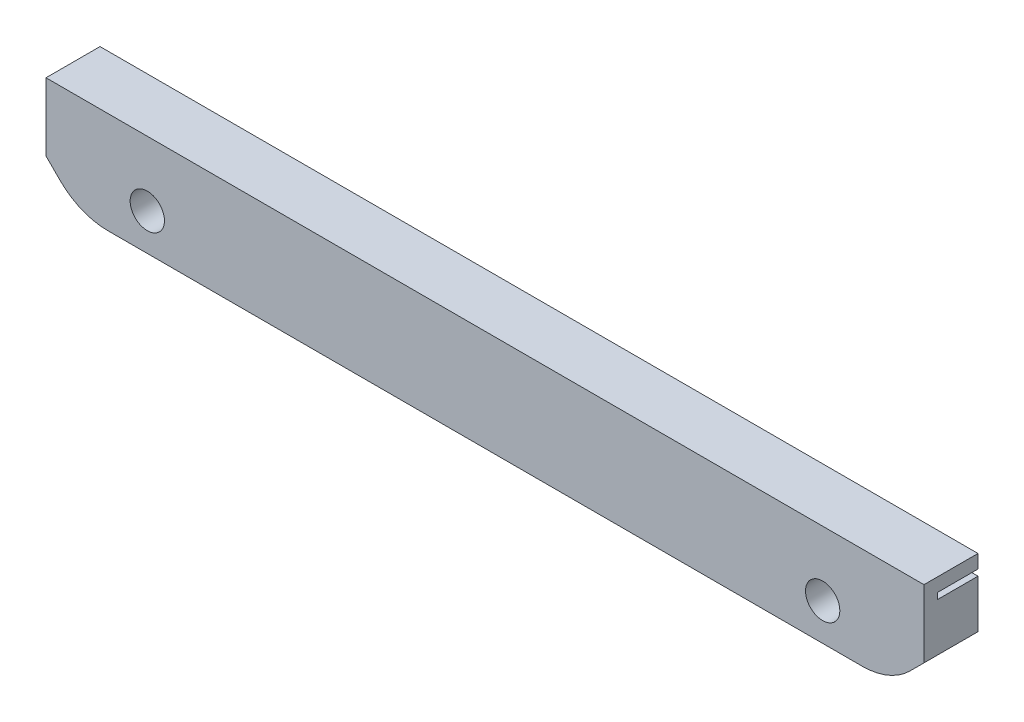
SolidWorks part; units mm, degrees
ref_plane "Front Plane" through (0, 0, 0) normal (0, 0, 1) x (1, 0, 0)
ref_plane "Top Plane" through (0, 0, 0) normal (0, 1, 0) x (1, 0, 0)
ref_plane "Right Plane" through (0, 0, 0) normal (1, 0, 0) x (0, 0, -1)
sketch "Sketch2" plane through (0, 0, 0) normal (0, 0, 1) x (1, 0, 0)
  line L0 (-115, -10) -> (-115, 135.26) construction
  line L1 (-115, 69.83) -> (15, 69.83)
  line L5 (15, 69.83) -> (15, 54.7963)
  line L6 (15, 54.7963) -> (-115, 54.7963)
  line L7 (-109.2, 69.93) -> (-66.71, 69.93) construction
  line L8 (-115, 54.7963) -> (-115, 69.83)
  circle A0 centre (-100, 60.26) radius 2.54
  circle A1 centre (0, 60.26) radius 2.54
  point P4 (-50, 29.465)
  dimension "D2" = 5.08
  dimension "D3" = 5.08
  dimension "D1" = 0.1
extrude "Boss-Extrude1" add sketch "Sketch2" along normal blind 6
sketch "Sketch3" plane through (0, 0, 6) normal (0, 0, 1) x (1, 0, 0)
  line L0 (15, 69.83) -> (-115, 69.83) construction
  line L5 (-59.5285, 67.83) -> (-59.5285, 59.3047)
  line L6 (-103.0137, 66.919) -> (-102.0149, 66.919)
  line L7 (-102.0149, 66.919) -> (-102.0149, 66.2967)
  line L8 (-102.0149, 66.2967) -> (-101.016, 66.2967)
  line L9 (-101.016, 66.2967) -> (-101.016, 66.919)
  line L10 (-101.016, 66.919) -> (-100.0172, 66.919)
  line L11 (-100.0172, 66.919) -> (-100.0172, 66.2967)
  line L12 (-100.0172, 66.2967) -> (-99.0183, 66.2967)
  line L13 (-99.0183, 66.2967) -> (-99.0183, 66.919)
  line L14 (-99.0183, 66.919) -> (-98.0195, 66.919)
  line L15 (-98.0195, 66.919) -> (-98.0195, 66.2967)
  line L16 (-98.0195, 66.2967) -> (-97.0206, 66.2967)
  line L17 (-97.0206, 66.2967) -> (-97.0206, 66.919)
  line L18 (-97.0206, 66.919) -> (-96.0218, 66.919)
  line L19 (-96.0218, 66.919) -> (-96.0218, 66.2967)
  line L20 (-96.0218, 66.2967) -> (-95.0229, 66.2967)
  line L21 (-95.0229, 66.2967) -> (-95.0229, 66.919)
  line L22 (-95.0229, 66.919) -> (-94.024, 66.919)
  line L23 (-94.024, 66.919) -> (-94.024, 66.2967)
  line L24 (-94.024, 66.2967) -> (-93.0252, 66.2967)
  line L25 (-93.0252, 66.2967) -> (-93.0252, 66.919)
  line L26 (-93.0252, 66.919) -> (-92.0263, 66.919)
  line L27 (-92.0263, 66.919) -> (-92.0263, 66.2967)
  line L28 (-92.0263, 66.2967) -> (-91.0275, 66.2967)
  line L29 (-91.0275, 66.2967) -> (-91.0275, 66.919)
  line L30 (-91.0275, 66.919) -> (-90.0286, 66.919)
  line L31 (-90.0286, 66.919) -> (-90.0286, 66.2967)
  line L32 (-90.0286, 66.2967) -> (-89.0298, 66.2967)
  line L33 (-89.0298, 66.2967) -> (-89.0298, 66.919)
  line L34 (-89.0298, 66.919) -> (-88.0309, 66.919)
  line L35 (-88.0309, 66.919) -> (-88.0309, 66.2967)
  line L36 (-88.0309, 66.2967) -> (-87.0321, 66.2967)
  line L37 (-87.0321, 66.2967) -> (-87.0321, 66.919)
  line L38 (-87.0321, 66.919) -> (-86.0332, 66.919)
  line L39 (-86.0332, 66.919) -> (-86.0332, 66.2967)
  line L40 (-86.0332, 66.2967) -> (-85.0344, 66.2967)
  line L41 (-85.0344, 66.2967) -> (-85.0344, 66.919)
  line L42 (-85.0344, 66.919) -> (-84.0355, 66.919)
  line L43 (-84.0355, 66.919) -> (-84.0355, 66.2967)
  line L44 (-84.0355, 66.2967) -> (-83.0366, 66.2967)
  line L45 (-83.0366, 66.2967) -> (-83.0366, 66.919)
  line L46 (-83.0366, 66.919) -> (-82.0378, 66.919)
  line L47 (-82.0378, 66.919) -> (-82.0378, 66.2967)
  line L48 (-82.0378, 66.2967) -> (-81.0389, 66.2967)
  line L49 (-81.0389, 66.2967) -> (-81.0389, 66.919)
  line L50 (-81.0389, 66.919) -> (-80.0401, 66.919)
  line L51 (-80.0401, 66.919) -> (-80.0401, 66.2967)
  line L52 (-80.0401, 66.2967) -> (-79.0412, 66.2967)
  line L53 (-79.0412, 66.2967) -> (-79.0412, 66.919)
  line L54 (-79.0412, 66.919) -> (-78.0424, 66.919)
  line L55 (-78.0424, 66.919) -> (-78.0424, 66.2967)
  line L56 (-78.0424, 66.2967) -> (-77.0435, 66.2967)
  line L57 (-77.0435, 66.2967) -> (-77.0435, 66.919)
  line L58 (-77.0435, 66.919) -> (-76.0447, 66.919)
  line L59 (-76.0447, 66.919) -> (-76.0447, 66.2967)
  line L60 (-76.0447, 66.2967) -> (-75.0458, 66.2967)
  line L61 (-75.0458, 66.2967) -> (-75.0458, 66.919)
  line L62 (-75.0458, 66.919) -> (-74.0469, 66.919)
  line L63 (-74.0469, 66.919) -> (-74.0469, 66.2967)
  line L64 (-74.0469, 66.2967) -> (-73.0481, 66.2967)
  line L65 (-73.0481, 66.2967) -> (-73.0481, 66.919)
  line L66 (-73.0481, 66.919) -> (-72.0492, 66.919)
  line L67 (-72.0492, 66.919) -> (-72.0492, 66.2967)
  line L68 (-72.0492, 66.2967) -> (-71.0504, 66.2967)
  line L69 (-71.0504, 66.2967) -> (-71.0504, 66.919)
  line L70 (-71.0504, 66.919) -> (-70.0515, 66.919)
  line L71 (-70.0515, 66.919) -> (-70.0515, 66.2967)
  line L72 (-70.0515, 66.2967) -> (-69.0527, 66.2967)
  line L73 (-69.0527, 66.2967) -> (-69.0527, 66.919)
  line L74 (-69.0527, 66.919) -> (-68.0538, 66.919)
  line L75 (-68.0538, 66.919) -> (-68.0538, 66.2967)
  line L76 (-68.0538, 66.2967) -> (-67.055, 66.2967)
  line L77 (-67.055, 66.2967) -> (-67.055, 66.919)
  line L78 (-67.055, 66.919) -> (-66.0561, 66.919)
  line L79 (-66.0561, 66.919) -> (-66.0561, 66.2967)
  line L80 (-66.0561, 66.2967) -> (-65.0573, 66.2967)
  line L81 (-65.0573, 66.2967) -> (-65.0573, 66.919)
  line L82 (-65.0573, 66.919) -> (-64.0584, 66.919)
  line L83 (-64.0584, 66.919) -> (-64.0584, 66.2967)
  line L84 (-64.0584, 66.2967) -> (-63.0595, 66.2967)
  line L85 (-63.0595, 66.2967) -> (-63.0595, 66.919)
  line L86 (-63.0595, 66.919) -> (-62.0607, 66.919)
  line L87 (-62.0607, 66.919) -> (-62.0607, 66.2967)
  line L88 (-62.0607, 66.2967) -> (-61.0618, 66.2967)
  line L89 (-61.0618, 66.2967) -> (-61.0618, 65.2979)
  line L90 (-61.0618, 65.2979) -> (-60.4395, 65.2979)
  line L91 (-60.4395, 65.2979) -> (-60.4395, 64.299)
  line L92 (-60.4395, 64.299) -> (-61.0618, 64.299)
  line L93 (-61.0618, 64.299) -> (-61.0618, 63.3001)
  line L94 (-61.0618, 63.3001) -> (-60.4395, 63.3001)
  line L95 (-60.4395, 63.3001) -> (-60.4395, 62.3013)
  line L96 (-60.4395, 62.3013) -> (-61.0618, 62.3013)
  line L97 (-61.0618, 62.3013) -> (-61.0618, 61.3024)
  line L98 (-61.0618, 61.3024) -> (-60.4395, 61.3024)
  line L99 (-60.4395, 61.3024) -> (-60.4395, 60.3036)
  line L100 (-60.4395, 60.3036) -> (-61.0618, 60.3036)
  line L101 (-61.0618, 60.3036) -> (-61.0618, 59.3047)
  line L102 (-61.0618, 59.3047) -> (-59.5285, 59.3047)
  line L103 (-103.0137, 66.919) -> (-103.0137, 66.2967)
  line L107 (-103.0137, 66.2967) -> (-104.0126, 66.2967)
  line L108 (-104.0126, 66.2967) -> (-104.0126, 66.919)
  line L109 (-104.0126, 66.919) -> (-105.0115, 66.919)
  line L110 (-105.0115, 66.919) -> (-105.0115, 66.2967)
  line L111 (-105.0115, 66.2967) -> (-106.0103, 66.2967)
  line L112 (-106.0103, 66.2967) -> (-106.0103, 66.919)
  line L113 (-106.0103, 66.919) -> (-107.0092, 66.919)
  line L114 (-107.0092, 66.919) -> (-107.0092, 66.2967)
  line L115 (-107.0092, 66.2967) -> (-108.008, 66.2967)
  line L116 (-108.008, 66.2967) -> (-108.008, 66.919)
  line L117 (-108.008, 66.919) -> (-109.0069, 66.919)
  line L118 (-109.0069, 66.919) -> (-109.0069, 66.2967)
  line L119 (-109.0069, 66.2967) -> (-110.0057, 66.2967)
  line L120 (-110.0057, 66.2967) -> (-110.0057, 66.919)
  line L121 (-110.0057, 66.919) -> (-111.0046, 66.919)
  line L122 (-111.0046, 66.919) -> (-111.0046, 66.2967)
  line L123 (-111.0046, 66.2967) -> (-112.0034, 66.2967)
  line L124 (-112.0034, 66.2967) -> (-112.0034, 66.919)
  line L125 (-112.0034, 66.919) -> (-113.0023, 66.919)
  line L126 (-113.0023, 66.919) -> (-113.0023, 66.2967)
  line L127 (-113.0023, 66.2967) -> (-114.0011, 66.2967)
  line L128 (-114.0011, 66.2967) -> (-114.0011, 66.919)
  line L137 (-115, 69.83) -> (-115, 54.7963) construction
  line L138 (-115, 66.919) -> (-115, 67.83)
  line L139 (-115, 67.83) -> (-59.5285, 67.83)
  line L140 (-114.0011, 66.919) -> (-115, 66.919)
  point P0 (-115, 67.7876)
  point P107 (-115, 65.3347)
  point P134 (-115.0643, 65.3347)
  dimension "D1" = 1.9977
  dimension "D2" = 1.5333
  dimension "D3" = 0.6223
  dimension "D4" = 1.5333
  dimension "D5" = 2
extrude "Cut-Extrude1" cut sketch "Sketch3" against normal through all
ref_plane "Plane1" through (-50, 0, 0) normal (1, 0, 0) x (0, 0, -1)
mirror "Mirror1" about plane through (-50, 0, 0) normal (1, 0, 0) of "Cut-Extrude1"
sketch "Sketch5" plane through (0, 0, 6) normal (0, 0, 1) x (1, 0, 0)
  line L1 (-115, 69.83) -> (15, 69.83)
  line L2 (-115, 69.83) -> (-115, 54.7963)
  line L3 (-115, 54.7963) -> (15, 54.7963)
  line L4 (15, 69.83) -> (15, 54.7963)
  line L5 (-115, 69.83) -> (15, 54.7963) construction
  line L6 (-115, 54.7963) -> (15, 69.83) construction
  circle A0 centre (-100, 60.26) radius 2.54
  circle A2 centre (0, 60.26) radius 2.54
  point P4 (-50, 62.3131)
extrude "Boss-Extrude2" add sketch "Sketch5" along normal blind 2
chamfer "Chamfer1" distance 5 angle 45 2 edges at (-115, 54.7963, 4) (15, 54.7963, 4)
fillet "Fillet1" radius 10 2 edges at (10, 54.7963, 4) (-110, 54.7963, 4)
